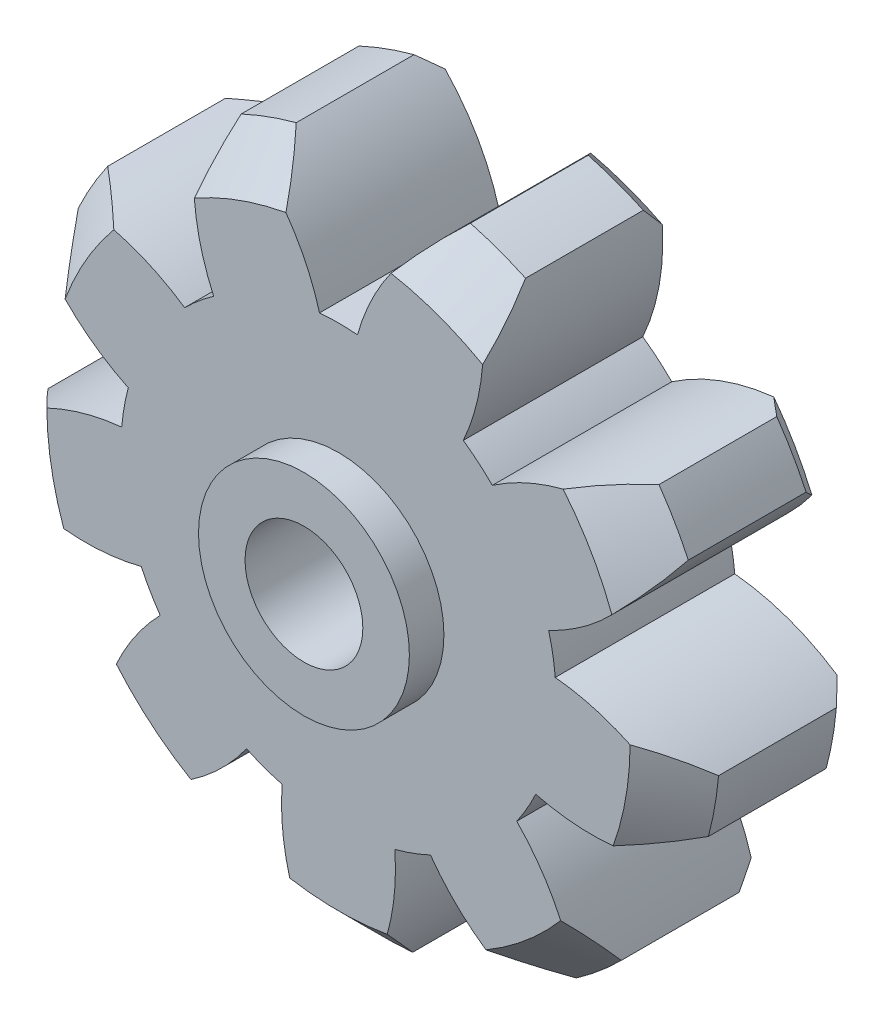
SolidWorks part; units mm, degrees
extrude "Gear Blank" add sketch "Sketch1" along normal mid plane 8
sketch "Sketch1" plane through (0, 0, 0) normal (0, 0, 1) x (1, 0, 0)
  circle A0 centre (0, 0) radius 15
  dimension "D1" = 30
chamfer "Front Gear Chamfer" distance 2 angle 45 1 edges at (15, 0, 4)
ref_plane "Plane1" through (0, 0, 0) normal (0, 0, 1) x (1, 0, 0)
ref_plane "Plane2" through (0, 0, 0) normal (0, 1, 0) x (-1, 0, 0)
ref_plane "Plane3" through (0, 0, 0) normal (1, 0, 0) x (0, 0, -1)
chamfer "Rear Gear Chamfer" distance 0.75 angle 45 1 edges at (15, 0, -4)
sketch "Sketch2" plane through (0, 0, 0) normal (0, 0, 1) x (1, 0, 0)
  line L0 (0, 15) -> (0, 0) construction
  line L1 (0, 0) -> (9.6524, 0) construction
  line L2 (0, 0) -> (-3.8823, 14.4889) construction
  line L3 (0, 0) -> (3.8823, 14.4889) construction
  line L4 (0, 0) -> (0.8454, 9.6631) construction
  line L5 (0, 0) -> (-0.8454, 9.6631) construction
  arc A1 (3.8823, 14.4889) -> (-3.8823, 14.4889) centre (0, 0) ccw
  arc A2 (3.8823, 14.4889) -> (0.8454, 9.6631) centre (10.4762, 6.9709) ccw
  arc A3 (-3.8823, 14.4889) -> (-0.8454, 9.6631) centre (-10.4762, 6.9709) cw
  arc A4 (-0.8454, 9.6631) -> (0.8454, 9.6631) centre (0, 0) cw
  circle A5 centre (0, 0) radius 15 construction
  dimension "D2" = 10
  dimension "D1" = 19.4
extrude "Tooth Cut" cut sketch "Sketch2" against normal mid plane 8
pattern_circular "Tooth Copies" count 9 every 40 about axis through (0, 0, 0) along (0, 0, 1) of "Tooth Cut"
sketch "Sketch3" plane through (0, 0, 4) normal (0, 0, 1) x (1, 0, 0)
  circle A0 centre (0, 0) radius 4.7
  arc A1 (1.4133, -4.4825) -> (1.7986, -4.3422) centre (0, 0) ccw construction
extrude "Boss-Extrude1" add sketch "Sketch3" along normal blind 1.54
sketch "Sketch4" plane through (0, 0, -4) normal (0, 0, -1) x (-1, 0, 0)
  circle A1 centre (0, 0) radius 2.625
  dimension "D1" = 5.25
extrude "Cut-Extrude1" cut sketch "Sketch4" against normal blind 10
equation "\"D2@Tooth Copies\"=360/\"D1@Tooth Copies\""
equation "\"D4@Sketch2\" = (3/4) * \"D2@Tooth Copies\""
equation "\"D5@Sketch2\"= \"D2@Tooth Copies\" - \"D4@Sketch2\""
equation "\"D1@Sketch2\" = \"D1@Sketch1\" - 10.6"
equation "\"D1@Tooth Cut\" = \"D1@Gear Blank\""
